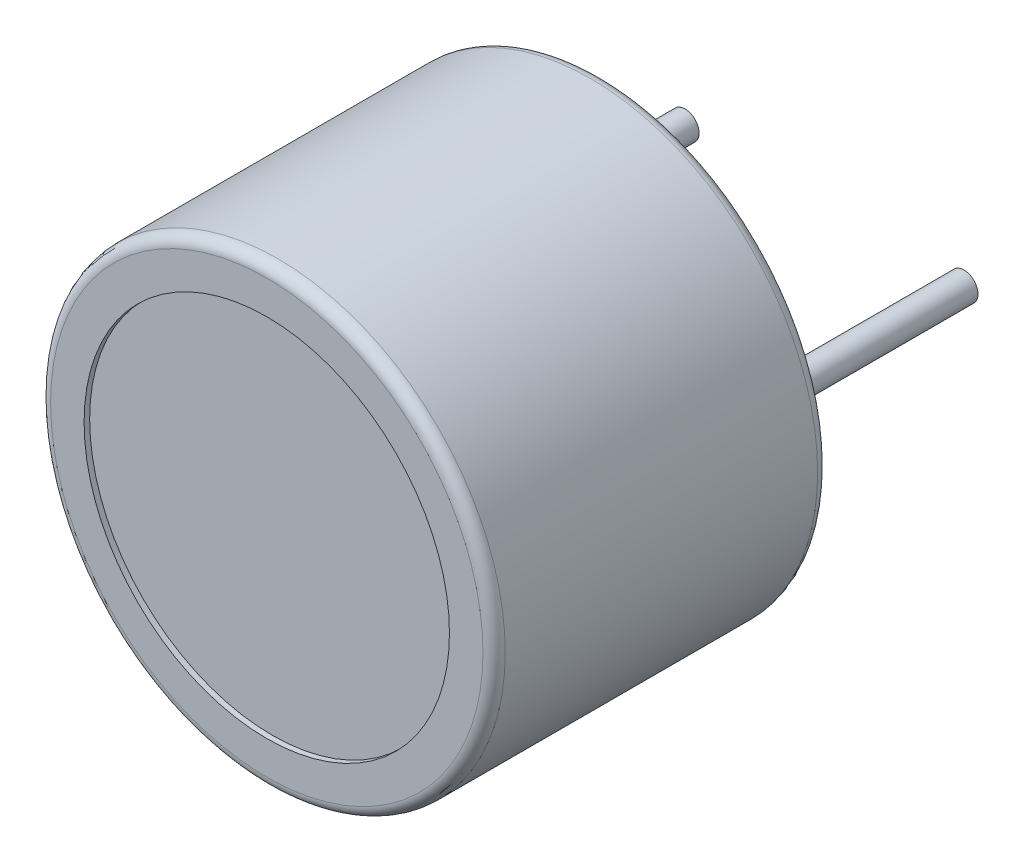
SolidWorks part; units mm, degrees
ref_plane "Plan de face" through (0, 0, 0) normal (0, 0, 1) x (1, 0, 0)
ref_plane "Plan de dessus" through (0, 0, 0) normal (0, 1, 0) x (1, 0, 0)
ref_plane "Plan de droite" through (0, 0, 0) normal (1, 0, 0) x (0, 0, -1)
sketch "EsqCorps" plane through (0, 0, 0) normal (0, 0, 1) x (1, 0, 0)
  circle A0 centre (0, 0) radius 8.15
  dimension "D1" = 16.3
extrude "Corps" add sketch "EsqCorps" along normal blind 12
sketch "EsqPattes" plane through (0, 0, 0) normal (0, 0, -1) x (-1, 0, 0)
  line L0 (-8.15, 0) -> (8.15, 0) construction
  line L1 (0, -8.15) -> (0, 8.15) construction
  circle A0 centre (-5, 0) radius 0.5
  circle A1 centre (5, 0) radius 0.5
  circle A2 centre (0, 0) radius 8.15 construction
  dimension "D1" = 1
  dimension "D2" = 5
extrude "Pattes" add sketch "EsqPattes" along normal blind 8
fillet "Congé1" radius 0.4 4 edges at (-4.5, 0, 0) (5.5, 0, 0) (8.15, 0, 0) (8.15, 0, 12)
sketch "EsqDevant" plane through (0, 0, 12) normal (0, 0, 1) x (1, 0, 0)
  circle A0 centre (0, 0) radius 6.55
  circle A1 centre (0, 0) radius 8.15 construction
  dimension "D1" = 1.6
extrude "Devant" cut sketch "EsqDevant" against normal blind 0.2
